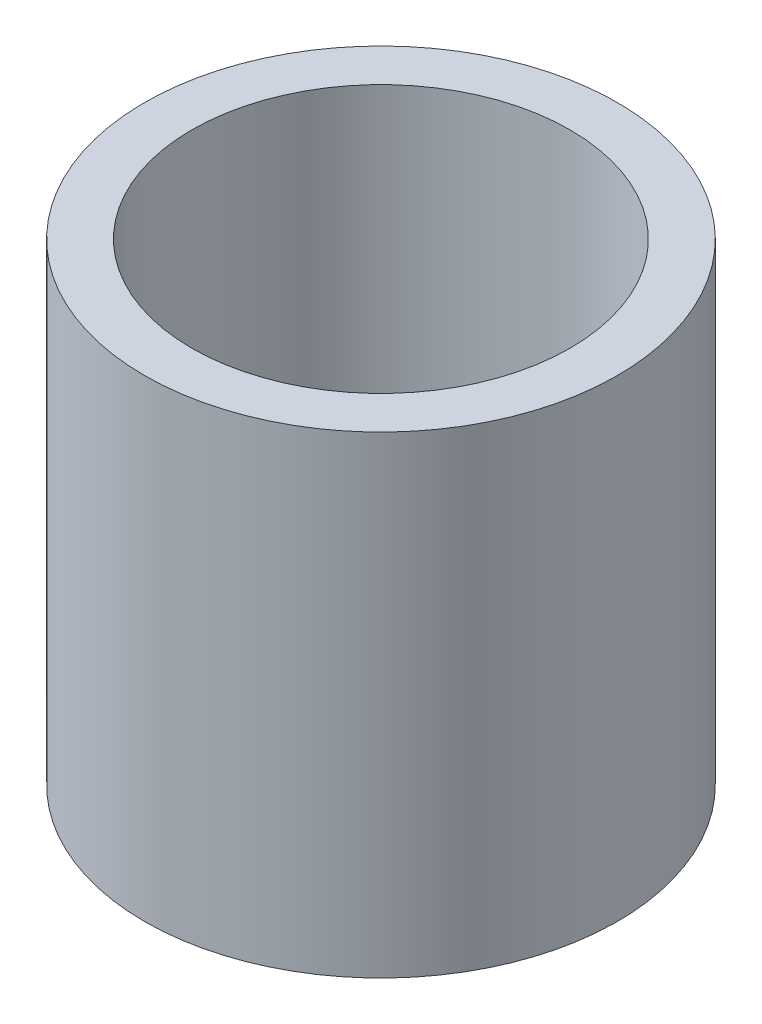
SolidWorks part; units mm, degrees
ref_plane "Front Plane" through (0, 0, 0) normal (0, 0, 1) x (1, 0, 0)
ref_plane "Top Plane" through (0, 0, 0) normal (0, 1, 0) x (1, 0, 0)
ref_plane "Right Plane" through (0, 0, 0) normal (1, 0, 0) x (0, 0, -1)
sketch "Sketch1" plane through (0, 0, 0) normal (0, 1, 0) x (1, 0, 0)
  circle A0 centre (0, 0) radius 5
  circle A1 centre (0, 0) radius 4
  dimension "D1" = 8
  dimension "D2" = 10
extrude "Boss-Extrude1" add sketch "Sketch1" along normal blind 10
